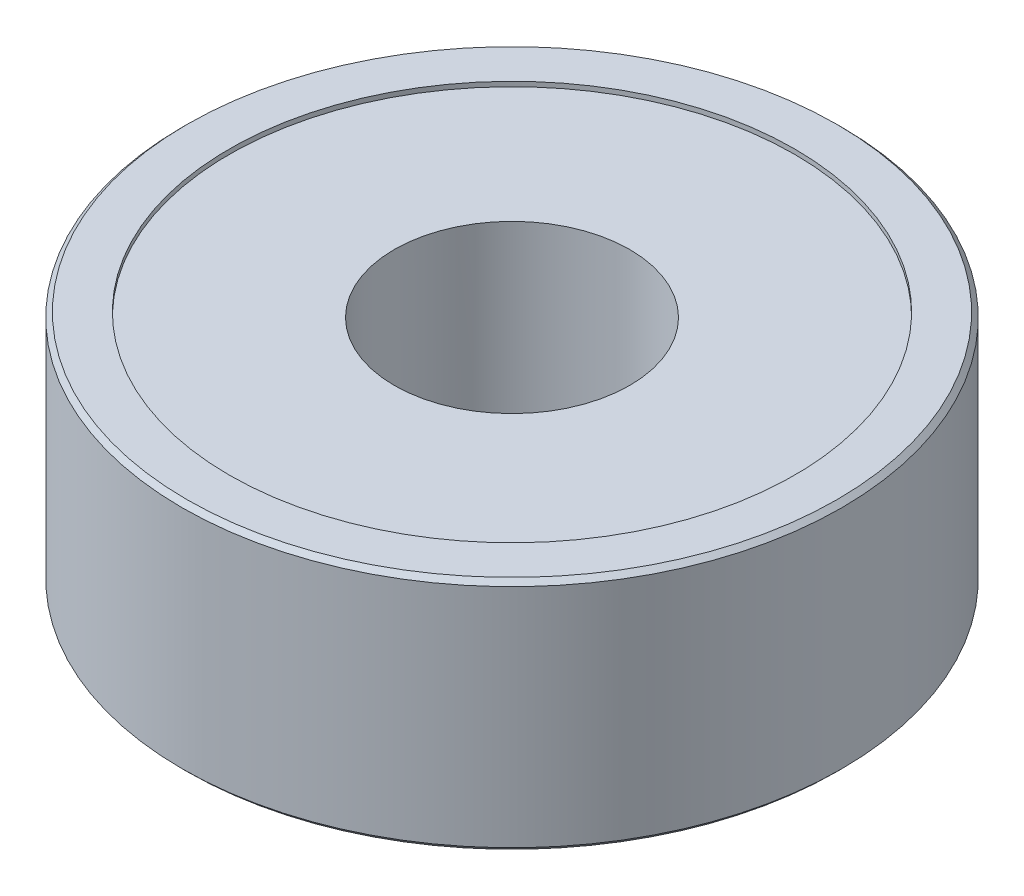
SolidWorks part; units mm, degrees
material "Cast Stainless Steel"
ref_plane "Front Plane" through (0, 0, 0) normal (0, 0, 1) x (1, 0, 0)
ref_plane "Top Plane" through (0, 0, 0) normal (0, 1, 0) x (1, 0, 0)
ref_plane "Right Plane" through (0, 0, 0) normal (1, 0, 0) x (0, 0, -1)
sketch "Sketch1" plane through (0, 0, 0) normal (0, 1, 0) x (1, 0, 0)
  circle A0 centre (0, 0) radius 2.5
  circle A1 centre (0, 0) radius 7
  dimension "D1" = 5
  dimension "D2" = 14
extrude "Boss-Extrude1" add sketch "Sketch1" along normal blind 5
sketch "Sketch2" plane through (0, 5, 0) normal (0, 1, 0) x (1, 0, 0)
  circle A0 centre (0, 0) radius 6
  dimension "D1" = 12
extrude "Cut-Extrude1" cut sketch "Sketch2" against normal blind 0.1
sketch "Sketch3" plane through (0, 0, 0) normal (0, -1, 0) x (1, 0, 0)
  circle A0 centre (0, 0) radius 6
  dimension "D1" = 12
extrude "Cut-Extrude2" cut sketch "Sketch3" against normal blind 0.1
chamfer "Chamfer1" distance 0.1 angle 45 2 edges at (0, 5, 7) (0, 0, 7)
